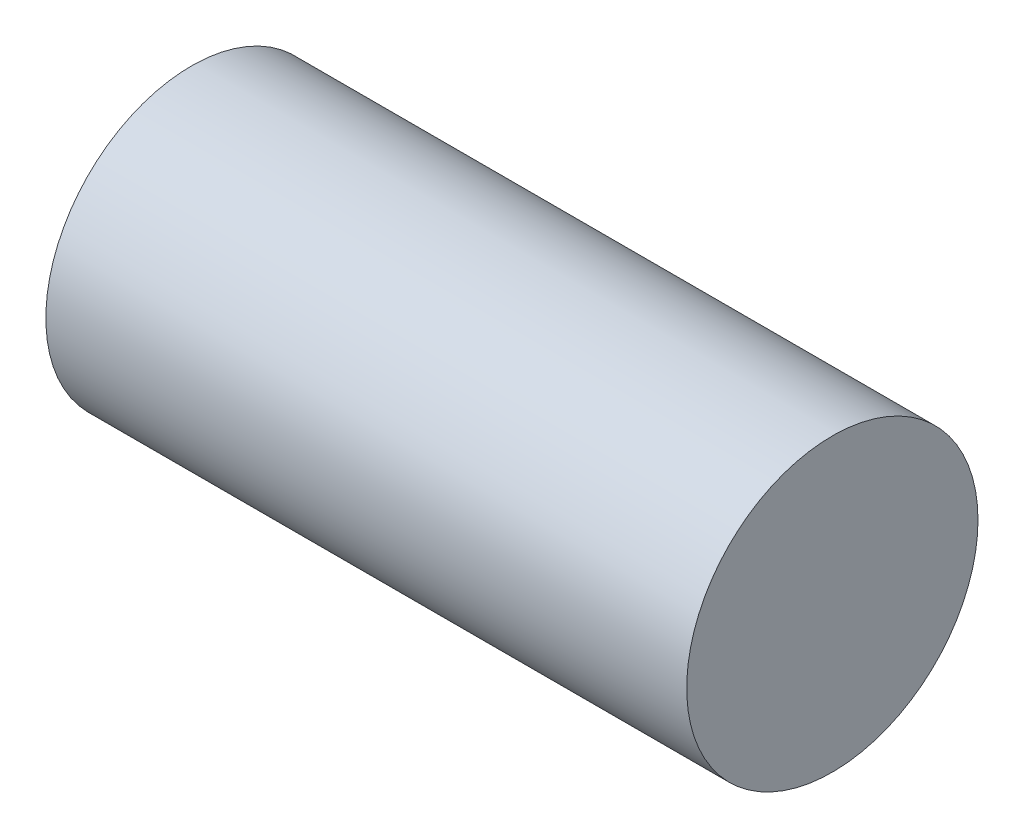
SolidWorks part; units mm, degrees
ref_plane "Front" through (0, 0, 0) normal (0, 0, 1) x (1, 0, 0)
ref_plane "Top" through (0, 0, 0) normal (0, 1, 0) x (1, 0, 0)
ref_plane "Right" through (0, 0, 0) normal (1, 0, 0) x (0, 0, -1)
sketch "Sketch1" plane through (0, 0, 0) normal (1, 0, 0) x (0, 0, -1)
  circle A0 centre (0, 0) radius 1.27
  dimension "D1" = 2.54
extrude "Boss-Extrude1" add sketch "Sketch1" along normal blind 5.588
